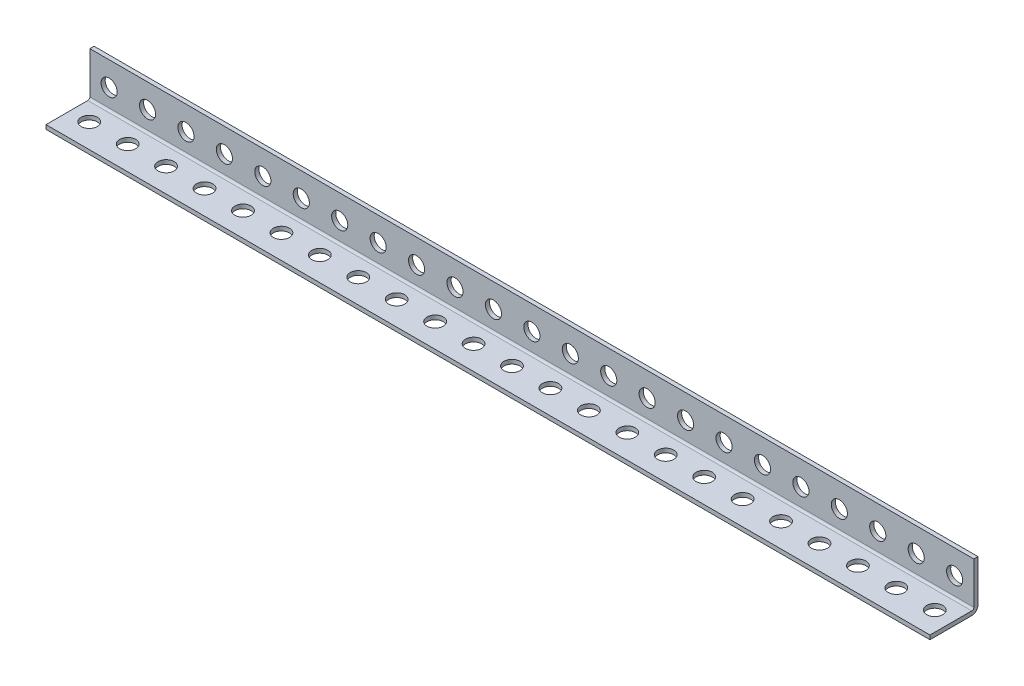
SolidWorks part; units mm, degrees
material "6061-T6 (SS)"
ref_plane "Front Plane" through (0, 0, 0) normal (0, 0, 1) x (1, 0, 0)
ref_plane "Top Plane" through (0, 0, 0) normal (0, 1, 0) x (1, 0, 0)
ref_plane "Right Plane" through (0, 0, 0) normal (1, 0, 0) x (0, 0, -1)
sketch "Sketch1" plane through (0, 0, 0) normal (1, 0, 0) x (0, 0, -1)
  line L0 (-15.875, -13.1318) -> (13.1318, -13.1318) construction
  line L1 (13.1318, -13.1318) -> (13.1318, 15.875) construction
  line L2 (13.1318, 15.875) -> (15.875, 15.875) construction
  line L3 (15.875, 15.875) -> (15.875, -15.875) construction
  line L4 (15.875, -15.875) -> (-15.875, -15.875) construction
  line L5 (-15.875, -15.875) -> (-15.875, -13.1318) construction
  line L6 (0, -15.875) -> (0, 15.875) construction
  line L7 (15.875, 0) -> (-15.875, 0) construction
  dimension "Thickness | T" = 2.7432
  dimension "Width (A)" = 31.75
  dimension "Width (B)" = 31.75
sketch "Sketch2" plane through (0, 0, 0) normal (0, 0, 1) x (1, 0, 0)
  line L0 (-609.6, 0) -> (609.6, 0) construction
  line L1 (-609.6, 15.875) -> (609.6, 15.875) construction
  line L2 (-609.6, 15.875) -> (-609.6, -15.875) construction
  line L3 (-609.6, -15.875) -> (609.6, -15.875) construction
  line L4 (609.6, 15.875) -> (609.6, -15.875) construction
  line L5 (0, 15.875) -> (0, -15.875) construction
  line L7 (-609.6, -13.1318) -> (609.6, -13.1318) construction
  circle A0 centre (596.9, 0) radius 5.334 construction
  circle A1 centre (571.5, 0) radius 5.334 construction
  point P15 (533.4, 0)
  point P16 (-533.4, 0)
  point P24 (602.234, 0)
  dimension "Mounting Hole Diameter" = 10.668
  dimension "Length | L" = 1219.2
  dimension "Mounting Hole Center to Center" = 25.4
  dimension "D1" = 12.7
  dimension "D2" = 63.5
sketch "Sketch3" plane through (0, 0, 0) normal (0, 1, 0) x (1, 0, 0)
  line L1 (-609.6, 15.875) -> (609.6, 15.875) construction
  line L2 (-609.6, 15.875) -> (-609.6, -15.875) construction
  line L3 (-609.6, -15.875) -> (609.6, -15.875) construction
  line L4 (609.6, 15.875) -> (609.6, -15.875) construction
  line L5 (-609.6, 13.1318) -> (609.6, 13.1318) construction
  line L7 (-609.6, 0) -> (609.6, 0) construction
  circle A0 centre (596.9, 0) radius 5.334 construction
  circle A1 centre (571.5, 0) radius 5.334 construction
  point P19 (-533.4, 0)
  point P21 (602.234, 0)
  point P22 (533.4, 0)
sketch "Sketch4" plane through (0, 0, 0) normal (1, 0, 0) x (0, 0, -1)
  line L0 (-15.875, -13.1318) -> (11.7602, -13.1318)
  line L1 (13.1318, -11.7602) -> (13.1318, 15.875)
  line L2 (13.1318, 15.875) -> (15.875, 15.875)
  line L3 (15.875, 15.875) -> (15.875, -11.7602)
  line L4 (11.7602, -15.875) -> (-15.875, -15.875)
  line L5 (-15.875, -15.875) -> (-15.875, -13.1318)
  line L6 (11.7602, -13.1318) -> (11.7602, -10.3886) construction
  arc A0 (11.7602, -13.1318) -> (13.1318, -11.7602) centre (11.7602, -11.7602) ccw
  arc A1 (15.875, -11.7602) -> (11.7602, -15.875) centre (11.7602, -11.7602) cw
extrude "Boss-Extrude1" add sketch "Sketch4" along normal up to vertex (609.6 mm away) and the other way up to vertex (609.6 mm away) up to point (609.6, 0, 0) other way up to point (-609.6, 0, 0)
sketch "Sketch5" plane through (0, 0, 0) normal (0, 0, 1) x (1, 0, 0)
  circle A0 centre (596.9, 0) radius 5.334
extrude "Cut-Extrude1" cut sketch "Sketch5" against normal through all
sketch "Sketch6" plane through (0, 0, 0) normal (0, 1, 0) x (1, 0, 0)
  circle A0 centre (596.9, 0) radius 5.334
extrude "Cut-Extrude2" cut sketch "Sketch6" against normal through all
pattern_linear "LPattern1" count 48 spacing 25.4 along (-1, 0, 0) of "Cut-Extrude2", "Cut-Extrude1"
sketch "Sketch7" plane through (0, 0, -15.875) normal (0, 0, -1) x (-1, 0, 0)
  line L0 (-609.6, -15.875) -> (609.6, -15.875) construction
  line L1 (-609.6, 15.875) -> (25.4, 15.875)
  line L2 (-609.6, 15.875) -> (-609.6, -15.875)
  line L3 (-609.6, -15.875) -> (25.4, -15.875)
  line L4 (25.4, 15.875) -> (25.4, -15.875)
  line L5 (602.234, 0) -> (609.6, 0) construction
  line L6 (609.6, -11.7602) -> (609.6, 15.875) construction
  line L7 (32.766, 0) -> (25.4, 0)
  circle A0 centre (596.9, 0) radius 5.334 construction
  circle A1 centre (38.1, 0) radius 5.334 construction
  dimension "D1" = 7.366
extrude "Cut-Extrude3" cut sketch "Sketch7" against normal blind 70 contours L4 L1 L2 L3
sketch "Sketch8" plane through (0, 0, -15.875) normal (0, 0, -1) x (-1, 0, 0)
  line L0 (602.234, 0) -> (609.6, 0)
  line L1 (609.6, -11.7602) -> (609.6, 15.875) construction
  line L2 (32.766, 0) -> (25.4, 0)
  line L3 (25.4, 15.875) -> (25.4, -11.7602) construction
  circle A0 centre (596.9, 0) radius 5.334 construction
  circle A1 centre (38.1, 0) radius 5.334 construction
sketch "Sketch9" plane through (0, -15.875, 0) normal (0, -1, 0) x (1, 0, 0)
  line L0 (-602.234, 0) -> (-609.6, 0)
  line L1 (-609.6, 15.875) -> (-609.6, -11.7602) construction
  line L2 (-32.766, 0) -> (-25.4, 0)
  line L3 (-25.4, 15.875) -> (-25.4, -11.7602) construction
  circle A0 centre (-596.9, 0) radius 5.334 construction
  circle A1 centre (-38.1, 0) radius 5.334 construction
equation "\"D1@Sketch2\"= ( \"Length | L@Sketch2\" - \"Mounting Hole Center to Center@Sketch2\" * \"Num Holes\" ) / 2"
equation "\"Num Holes\"= int ( \"Length | L@Sketch2\" / \"Mounting Hole Center to Center@Sketch2\" ) - 1"
equation "\"D2@Sketch2\"=\"Mounting Hole Center to Center@Sketch2\"*2.5"
equation "\"D3@LPattern1\"=\"Mounting Hole Center to Center@Sketch2\""
